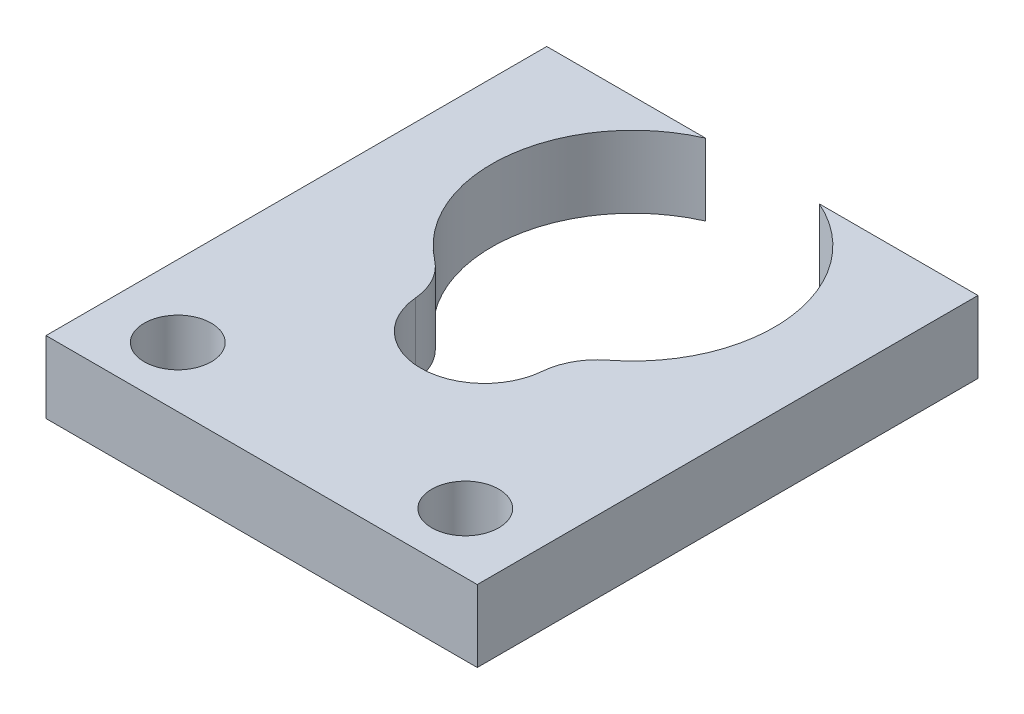
SolidWorks part; units mm, degrees
ref_plane "Alzado" through (0, 0, 0) normal (0, 0, 1) x (1, 0, 0)
ref_plane "Planta" through (0, 0, 0) normal (0, 1, 0) x (1, 0, 0)
ref_plane "Vista lateral" through (0, 0, 0) normal (1, 0, 0) x (0, 0, -1)
sketch "Croquis1" plane through (0, 0, 0) normal (0, 1, 0) x (1, 0, 0)
  line L0 (2.377, 5.4) -> (9, 5.4)
  line L5 (-9, 5.4) -> (-2.377, 5.4)
  line L6 (-9, 5.4) -> (-9, -15.5)
  line L7 (-9, -15.5) -> (9, -15.5)
  line L8 (9, 5.4) -> (9, -15.5)
  arc A2 (3.6108, -4.6661) -> (2.377, 5.4) centre (0, 0) ccw
  arc A3 (-2.65, -6.4285) -> (2.65, -6.4285) centre (0, -6.2) ccw
  circle A4 centre (-6, -13) radius 1.4
  circle A5 centre (6, -13) radius 1.4
  arc A6 (-2.377, 5.4) -> (-3.6108, -4.6661) centre (0, 0) ccw
  arc A7 (-2.65, -6.4285) -> (-3.6108, -4.6661) centre (-5.1408, -6.6432) ccw
  arc A8 (2.65, -6.4285) -> (3.6108, -4.6661) centre (5.1408, -6.6432) cw
  point P9 (0, -15.5)
  dimension "D1" = 5.9
  dimension "D3" = 5.3
  dimension "D4" = 18
  dimension "D7" = 2.8
  dimension "D8" = 13
  dimension "D6" = 2.5
  dimension "D11" = 2.5
  dimension "D12" = 2.5
  dimension "D2" = 6.2
  dimension "D5" = 5.4
  dimension "D9" = 6
  dimension "D10" = 6
extrude "Saliente-Extruir1" add sketch "Croquis1" along normal blind 3
